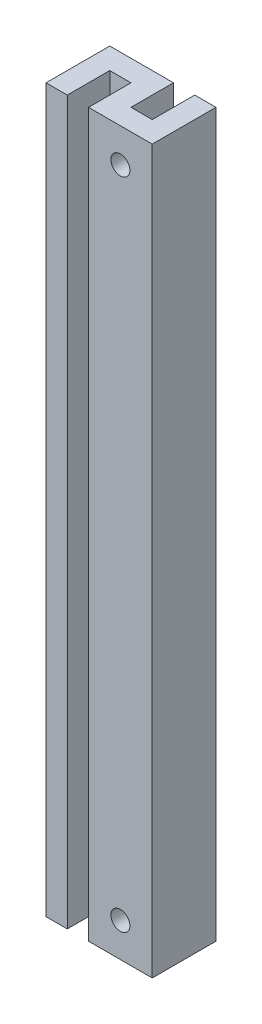
SolidWorks part; units mm, degrees
material "6061 Alloy"
ref_plane "Front Plane" through (0, 0, 0) normal (0, 0, 1) x (1, 0, 0)
ref_plane "Top Plane" through (0, 0, 0) normal (0, 1, 0) x (1, 0, 0)
ref_plane "Right Plane" through (0, 0, 0) normal (1, 0, 0) x (0, 0, -1)
sketch "Sketch1" plane through (0, 0, 0) normal (0, 1, 0) x (1, 0, 0)
  line L0 (-1.5875, -4.7625) -> (7.9375, -4.7625)
  line L1 (-7.9375, -4.7625) -> (-4.7625, -4.7625)
  line L2 (-7.9375, -4.7625) -> (-7.9375, 4.7625)
  line L3 (-7.9375, 4.7625) -> (1.5875, 4.7625)
  line L4 (7.9375, -4.7625) -> (7.9375, 4.7625)
  line L5 (-7.9375, -4.7625) -> (7.9375, 4.7625) construction
  line L6 (-7.9375, 4.7625) -> (7.9375, -4.7625) construction
  line L7 (4.7625, 4.7625) -> (7.9375, 4.7625)
  line L8 (-4.7625, -4.7625) -> (-4.7625, 1.5875)
  line L9 (-4.7625, 1.5875) -> (-1.5875, 1.5875)
  line L10 (-1.5875, -4.7625) -> (-1.5875, 1.5875)
  line L12 (1.5875, 4.7625) -> (1.5875, -1.5875)
  line L13 (1.5875, -1.5875) -> (4.7625, -1.5875)
  line L14 (4.7625, 4.7625) -> (4.7625, -1.5875)
  point P0 (0, 0)
  dimension "D1" = 9.525
  dimension "D2" = 15.875
  dimension "D3" = 3.175
  dimension "D4" = 3.175
  dimension "D5" = 3.175
  dimension "D6" = 3.175
  dimension "D7" = 3.175
  dimension "D8" = 3.175
extrude "Extrude1" add sketch "Sketch1" along normal mid plane 107.95
sketch "Sketch2" plane through (0, 0, 4.7625) normal (0, 0, 1) x (1, 0, 0)
  line L0 (3.175, 53.975) -> (3.175, -53.975) construction
  line L1 (-1.5875, 53.975) -> (7.9375, 53.975) construction
  line L2 (-1.5875, -53.975) -> (7.9375, -53.975) construction
  circle A0 centre (3.175, -48.895) radius 1.1303
  circle A1 centre (3.175, 48.895) radius 1.1303
  dimension "D2" = 2.2606
  dimension "D3" = 5.08
  dimension "D1" = 5.08
extrude "Extrude2" cut sketch "Sketch2" against normal through all
sketch "Sketch3" plane through (0, 0, -4.7625) normal (0, 0, -1) x (-1, 0, 0)
  line L0 (3.175, 53.975) -> (3.175, -53.975) construction
  line L1 (-1.5875, 53.975) -> (7.9375, 53.975) construction
  line L2 (-1.5875, -53.975) -> (7.9375, -53.975) construction
  circle A0 centre (3.175, 49.2125) radius 1.1303
  circle A1 centre (-3.175, -48.895) radius 1.1303 construction
  dimension "D1" = 4.7625
extrude "Extrude3" cut sketch "Sketch3" against normal up to next
hole_wizard "#4-40 Tapped Hole1" positions "3DSketch1" profile "Sketch4" tap size "#4-40" standard "Ansi Inch"
sketch3d "3DSketch1"
  line L0 (3.175, -48.895, 1.5875) -> (3.175, -48.895, 4.7625) construction
  line L1 (3.175, 48.895, 1.5875) -> (3.175, 48.895, 4.7625) construction
  point P0 (3.175, 48.895, 4.7625)
  point P2 (3.175, -48.895, 4.7625)
sketch "Sketch4" plane through (3.175, 48.895, 4.7625) normal (1, 0, 0) x (0, -1, 0)
  line L0 (0, 0) -> (0, 9.5692)
  line L1 (0, 9.5692) -> (1.1303, 8.89)
  line L2 (1.1303, 8.89) -> (1.1303, 5.588)
  line L3 (1.1303, 5.588) -> (1.4224, 5.588)
  line L4 (1.4224, 5.588) -> (1.4224, 0)
  line L5 (1.4224, 0) -> (0, 0)
  line L10 (0, 9.5692) -> (-1.1303, 8.89) construction
  line L11 (0, -6.35) -> (0, 107.95) construction
  dimension "Tap Drill Dia." = 2.2606
  dimension "Tap Drill Depth" = 8.89
  dimension "Thread Major Dia." = 2.8448
  dimension "Thread Depth" = 5.588
  dimension "Drill Angle" = 118
